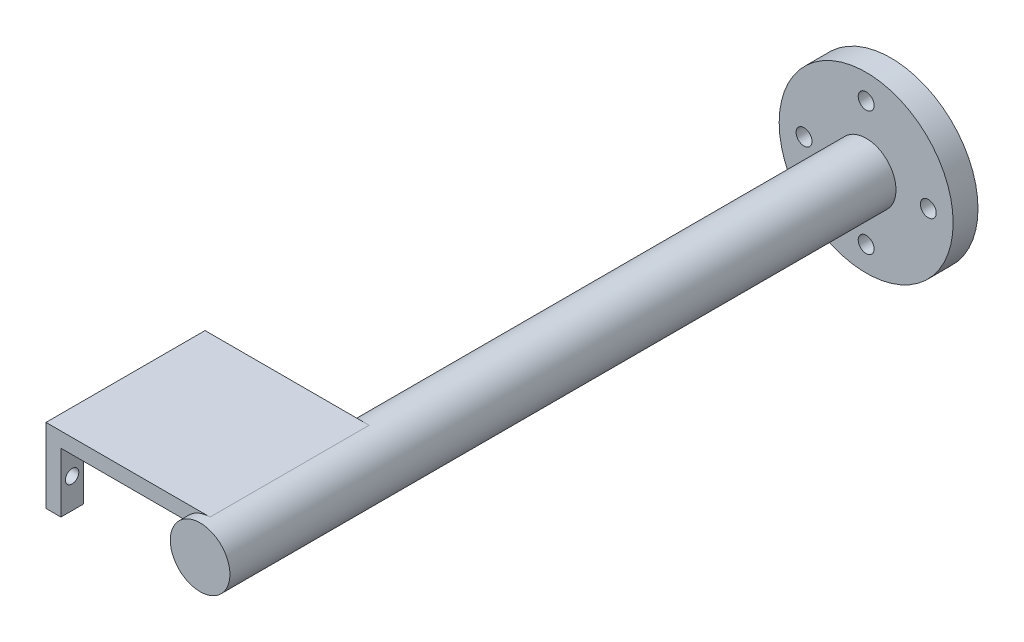
SolidWorks part; units mm, degrees
ref_plane "前视基准面" through (0, 0, 0) normal (0, 0, 1) x (1, 0, 0)
ref_plane "上视基准面" through (0, 0, 0) normal (0, 1, 0) x (1, 0, 0)
ref_plane "右视基准面" through (0, 0, 0) normal (1, 0, 0) x (0, 0, -1)
other "Configuration Table"
sketch "草图1" plane through (0, 0, 0) normal (0, 0, 1) x (1, 0, 0)
  line L0 (-32.4058, 8.6736) -> (-5.4058, 8.6736)
  line L1 (-4.6019, 5.6736) -> (-29.4058, 5.6736)
  line L2 (-5.4058, 8.6736) -> (-5.4058, 5.6736) construction
  line L3 (-32.4058, 5.6736) -> (-32.4058, 8.6736)
  line L4 (-5.4058, 8.6736) -> (0.5942, 8.6736)
  line L7 (-32.4058, 5.6736) -> (-32.4058, -6.3264)
  line L8 (-32.4058, -6.3264) -> (-29.4058, -6.3264)
  line L9 (-29.4058, 5.6736) -> (-29.4058, -6.3264)
  arc A0 (-4.6019, 5.6736) -> (0.5942, 8.6736) centre (0.5942, 2.6736) ccw
  circle A1 centre (0.5942, 2.6736) radius 4.1
  dimension "D1" = 12
  dimension "D2" = 8.2
  dimension "D3" = 3
  dimension "D4" = 27
  dimension "D5" = 3
  dimension "D6" = 12
extrude "凸台-拉伸1" add sketch "草图1" along normal blind 32
sketch "草图3" plane through (-32.4058, 0, 0) normal (-1, 0, 0) x (0, 0, 1)
  line L0 (0, 8.6736) -> (0, -6.3264) construction
  line L1 (32, -6.3264) -> (0, -6.3264) construction
  line L2 (32, -6.3264) -> (32, 5.6736) construction
  line L3 (32, 5.6736) -> (0, 5.6736) construction
  line L4 (0, -6.3264) -> (0, 5.6736) construction
  line L5 (32, 8.6736) -> (0, 8.6736) construction
  line L6 (27.5, 5.6736) -> (27.5, -6.3264)
  line L7 (4.5, 5.6736) -> (4.5, -6.3264)
  line L8 (27.5, -0.3264) -> (4.5, -0.3264) construction
  line L9 (16, 5.6736) -> (16, -6.3264) construction
  line L10 (27.5, 5.6736) -> (4.5, 5.6736)
  line L11 (4.5, -6.3264) -> (27.5, -6.3264)
  line L12 (27.5, -0.3264) -> (32, -0.3264) construction
  line L13 (4.5, -0.3264) -> (0, -0.3264) construction
  circle A0 centre (29.75, -0.3264) radius 1.35
  circle A1 centre (2.25, -0.3264) radius 1.35
  point P15 (16, -0.3264)
  dimension "D3" = 2.7
  dimension "D1" = 3
  dimension "D2" = 23
extrude "切除-拉伸1" cut sketch "草图3" against normal blind 5 contours L11 L6 L10 L7 | A0 | A1
sketch "草图4" plane through (0, 0, 0) normal (0, 1, 0) x (1, 0, 0)
  line L0 (0.5942, -32) -> (0.5942, 0) construction
  line L1 (-5.4058, -32) -> (6.5942, -32) construction
  circle A0 centre (0.5942, -4.3653) radius 1.6
  circle A1 centre (0.5942, -28.1239) radius 1.6
  dimension "D1" = 3.2
sketch "草图5" plane through (0, 0, 32) normal (0, 0, 1) x (1, 0, 0)
  circle A0 centre (0.5942, 2.6736) radius 6
extrude "凸台-拉伸2" add sketch "草图5" along normal blind 2
sketch "草图6" plane through (0, 0, 0) normal (0, 0, -1) x (-1, 0, 0)
  circle A0 centre (-0.5942, 2.6736) radius 4.1
  circle A1 centre (-0.5942, 2.6736) radius 6
extrude "凸台-拉伸3" add sketch "草图6" along normal blind 100 contours A1
sketch "草图7" plane through (0, 0, -100) normal (0, 0, -1) x (-1, 0, 0)
  circle A0 centre (-0.5942, 2.6736) radius 17.5
  dimension "D1" = 35
extrude "凸台-拉伸4" add sketch "草图7" along normal blind 5
sketch "草图9" plane through (0, 0, -105) normal (0, 0, -1) x (-1, 0, 0)
  circle A0 centre (-0.5942, 2.6736) radius 12.5 construction
  circle A1 centre (11.9058, 2.6736) radius 1.6
  circle A2 centre (-0.5942, 15.1736) radius 1.6
  circle A3 centre (-13.0942, 2.6736) radius 1.6
  circle A4 centre (-0.5942, -9.8264) radius 1.6
  dimension "D1" = 25
  dimension "D2" = 3.2
extrude "切除-拉伸3" cut sketch "草图9" against normal through all
